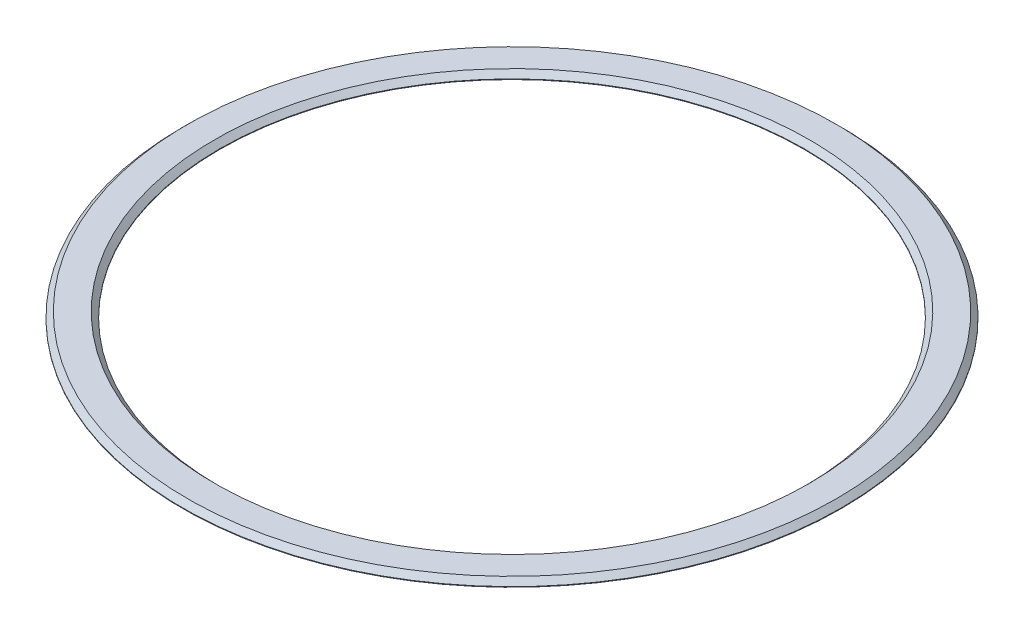
SolidWorks part; units mm, degrees
ref_plane "前视基准面" through (0, 0, 0) normal (0, 0, 1) x (1, 0, 0)
ref_plane "上视基准面" through (0, 0, 0) normal (0, 1, 0) x (1, 0, 0)
ref_plane "右视基准面" through (0, 0, 0) normal (1, 0, 0) x (0, 0, -1)
other "Configuration Table"
sketch "草图1" plane through (0, 0, 0) normal (0, 0, 1) x (1, 0, 0)
  line L0 (0, 0) -> (0, 63.0792) construction
  line L1 (0, 66.476) -> (0, -84.7734) construction
  line L2 (-113.7607, 8.4) -> (-113.7607, 8.2)
  line L3 (-113.7607, 8.2) -> (-100.9105, 8.2)
  line L4 (-100.9105, 8.2) -> (-100.9105, 8.4)
  line L6 (-114.3607, 94.7) -> (-114.3607, -9) construction
  line L7 (-100.9105, -8) -> (-100.9105, 0) construction
  line L8 (0, 0) -> (-171.2493, 0) construction
  line L9 (-113.7607, 8.4) -> (-111.9607, 10.2)
  line L10 (-111.9607, 10.2) -> (-102.7105, 10.2)
  line L11 (-102.7105, 10.2) -> (-100.9105, 8.4)
  dimension "D1" = 0.2
  dimension "D2" = 0.6
  dimension "D3" = 8.2
  dimension "D4" = 0.2
  dimension "D5" = 135
  dimension "D6" = 2
  dimension "D7" = 135
revolve "旋转1" add sketch "草图1" angle 360 about L0
